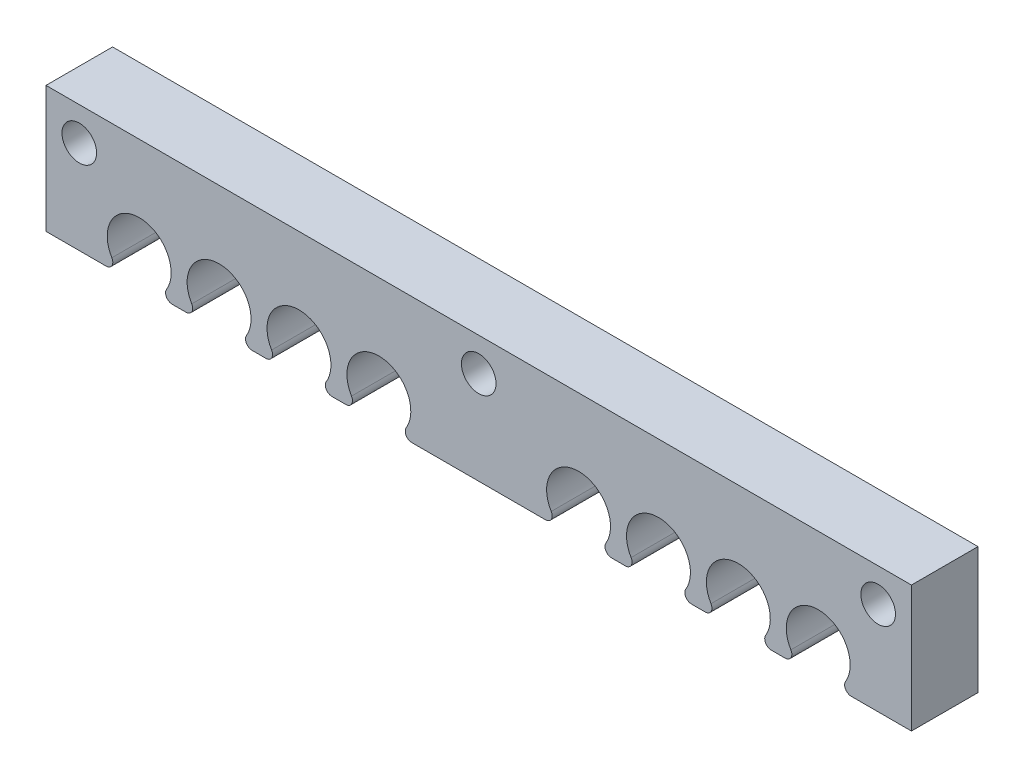
SolidWorks part; units mm, degrees
ref_plane "Front Plane" through (0, 0, 0) normal (0, 0, 1) x (1, 0, 0)
ref_plane "Top Plane" through (0, 0, 0) normal (0, 1, 0) x (1, 0, 0)
ref_plane "Right Plane" through (0, 0, 0) normal (1, 0, 0) x (0, 0, -1)
sketch "Sketch1" plane through (0, 0, 0) normal (0, 0, 1) x (1, 0, 0)
  line L0 (0, 0) -> (0, 19)
  line L1 (0, 19) -> (130, 19)
  line L2 (130, 19) -> (130, 0)
  line L3 (9.0361, 0) -> (0, 0)
  line L4 (21.0361, 0) -> (18.9639, 0)
  line L5 (33.0361, 0) -> (30.9639, 0)
  line L6 (45.0361, 0) -> (42.9639, 0)
  line L7 (75.0361, 0) -> (54.9639, 0)
  line L8 (87.0361, 0) -> (84.9639, 0)
  line L9 (99.0361, 0) -> (96.9639, 0)
  line L10 (111.0361, 0) -> (108.9639, 0)
  line L27 (130, 0) -> (120.9639, 0)
  line L28 (65, 4) -> (65, 19) construction
  circle A0 centre (5, 14) radius 2.6
  circle A1 centre (65, 14) radius 2.6
  circle A2 centre (125, 14) radius 2.6
  arc A3 (54.108, 1.5172) -> (45.892, 1.5172) centre (50, 4) ccw
  arc A4 (42.108, 1.5172) -> (33.892, 1.5172) centre (38, 4) ccw
  arc A5 (30.108, 1.5172) -> (21.892, 1.5172) centre (26, 4) ccw
  arc A6 (18.108, 1.5172) -> (9.892, 1.5172) centre (14, 4) ccw
  arc A7 (84.108, 1.5172) -> (75.892, 1.5172) centre (80, 4) ccw
  arc A8 (96.108, 1.5172) -> (87.892, 1.5172) centre (92, 4) ccw
  arc A9 (108.108, 1.5172) -> (99.892, 1.5172) centre (104, 4) ccw
  arc A10 (120.108, 1.5172) -> (111.892, 1.5172) centre (116, 4) ccw
  arc A11 (120.108, 1.5172) -> (120.9639, 0) centre (120.9639, 1) ccw
  arc A12 (111.892, 1.5172) -> (111.0361, 0) centre (111.0361, 1) cw
  arc A13 (108.108, 1.5172) -> (108.9639, 0) centre (108.9639, 1) ccw
  arc A14 (99.892, 1.5172) -> (99.0361, 0) centre (99.0361, 1) cw
  arc A15 (96.108, 1.5172) -> (96.9639, 0) centre (96.9639, 1) ccw
  arc A16 (87.892, 1.5172) -> (87.0361, 0) centre (87.0361, 1) cw
  arc A17 (84.108, 1.5172) -> (84.9639, 0) centre (84.9639, 1) ccw
  arc A18 (75.892, 1.5172) -> (75.0361, 0) centre (75.0361, 1) cw
  arc A19 (54.108, 1.5172) -> (54.9639, 0) centre (54.9639, 1) ccw
  arc A20 (45.892, 1.5172) -> (45.0361, 0) centre (45.0361, 1) cw
  arc A21 (42.108, 1.5172) -> (42.9639, 0) centre (42.9639, 1) ccw
  arc A22 (33.892, 1.5172) -> (33.0361, 0) centre (33.0361, 1) cw
  arc A23 (30.108, 1.5172) -> (30.9639, 0) centre (30.9639, 1) ccw
  arc A24 (21.892, 1.5172) -> (21.0361, 0) centre (21.0361, 1) cw
  arc A25 (18.108, 1.5172) -> (18.9639, 0) centre (18.9639, 1) ccw
  arc A26 (9.892, 1.5172) -> (9.0361, 0) centre (9.0361, 1) cw
  point P38 (113.3467, 0)
  point P46 (101.3467, 0)
  point P51 (89.3467, 0)
  point P56 (77.3467, 0)
  point P61 (47.3467, 0)
  point P66 (35.3467, 0)
  point P71 (23.3467, 0)
  point P76 (11.3467, 0)
  dimension "D8" = 5.2
  dimension "D16" = 9.6
  dimension "D18" = 1
  dimension "D2" = 15
  dimension "D3" = 12
  dimension "D4" = 19
  dimension "D5" = 130
  dimension "D6" = 12
  dimension "D7" = 5
  dimension "D9" = 5
  dimension "D10" = 5
  dimension "D11" = 12
  dimension "D12" = 12
  dimension "D13" = 12
  dimension "D14" = 15
  dimension "D15" = 15
  dimension "D17" = 12
extrude "Boss-Extrude1" add sketch "Sketch1" along normal blind 10
sketch "Sketch2" plane through (0, 0, 0) normal (0, -1, 0) x (1, 0, 0)
  line L0 (54.9639, 10) -> (75.0361, 10) construction
  line L1 (54.9639, 0) -> (75.0361, 10) construction
  line L2 (75.0361, 10) -> (75.0361, 0) construction
  circle A0 centre (4.6, 5) radius 2.6
  circle A1 centre (65, 5) radius 2.6
  circle A2 centre (125.4, 5) radius 2.6
  dimension "D1" = 5.2
  dimension "D2" = 60.4
  dimension "D3" = 60.4
extrude "Cut-Extrude1" cut sketch "Sketch2" against normal blind 8
